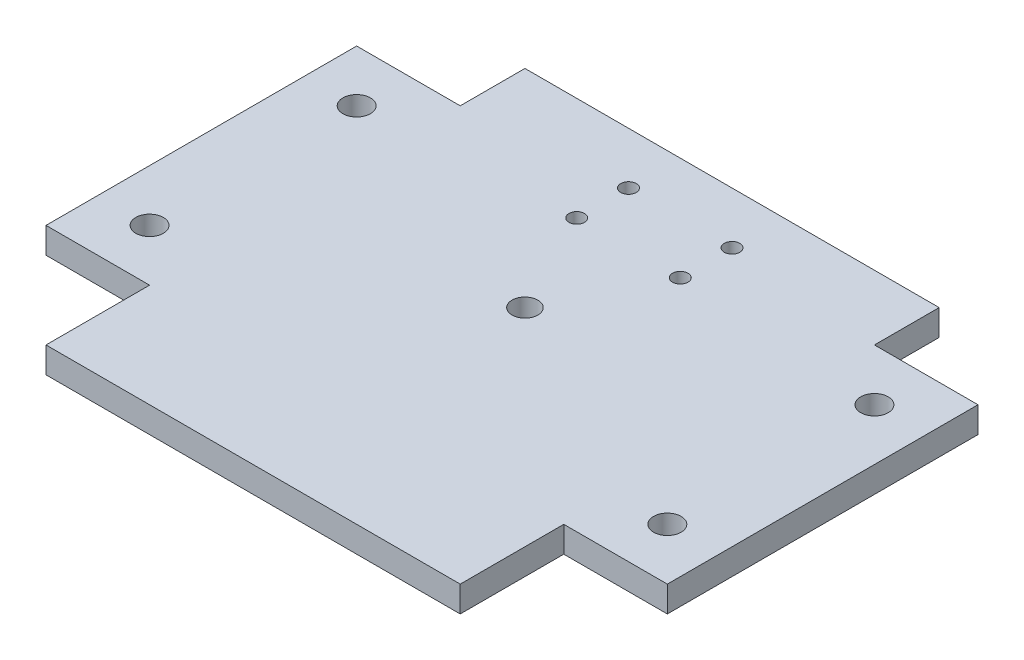
SolidWorks part; units mm, degrees
ref_plane "Front Plane" through (0, 0, 0) normal (0, 0, 1) x (1, 0, 0)
ref_plane "Top Plane" through (0, 0, 0) normal (0, 1, 0) x (1, 0, 0)
ref_plane "Right Plane" through (0, 0, 0) normal (1, 0, 0) x (0, 0, -1)
sketch "Sketch1" plane through (0, 0, 0) normal (0, 1, 0) x (1, 0, 0)
  line L0 (63.5, 104.775) -> (88.9, 104.775) construction
  line L1 (0, 0) -> (152.4, 0)
  line L2 (0, 0) -> (0, 117.475)
  line L3 (0, 117.475) -> (152.4, 117.475)
  line L4 (152.4, 0) -> (152.4, 117.475)
  line L7 (0, 101.6) -> (25.4, 101.6)
  line L8 (25.4, 117.475) -> (25.4, 101.6)
  line L11 (0, 25.4) -> (25.4, 25.4)
  line L12 (25.4, 0) -> (25.4, 25.4)
  line L15 (152.4, 101.6) -> (127, 101.6)
  line L16 (127, 117.475) -> (127, 101.6)
  line L19 (152.4, 25.4) -> (127, 25.4)
  line L20 (127, 0) -> (127, 25.4)
  line L21 (88.9, 104.775) -> (88.9, 92.075) construction
  line L22 (88.9, 92.075) -> (63.5, 92.075) construction
  line L23 (63.5, 92.075) -> (63.5, 104.775) construction
  circle A0 centre (12.7, 88.9) radius 3.3782
  circle A1 centre (139.7, 88.9) radius 3.3782
  circle A2 centre (12.7, 38.1) radius 3.3782
  circle A3 centre (139.7, 38.1) radius 3.3782
  circle A4 centre (63.5, 104.775) radius 1.905
  circle A5 centre (88.9, 104.775) radius 1.905
  circle A6 centre (63.5, 92.075) radius 1.905
  circle A7 centre (88.9, 92.075) radius 1.905
  circle A8 centre (76.2, 66.675) radius 3.175
  point P30 (12.7, 25.4)
  point P32 (139.7, 25.4)
  point P35 (76.2, 117.475)
  point P36 (76.2, 104.775)
  point P39 (0, 0)
  point P40 (76.2, 92.075)
  point P41 (0, 0)
  point P42 (0, 0)
  point P43 (0, 0)
  point P44 (0, 0)
  point P45 (0, 0)
  point P46 (0, 0)
  point P47 (0, 0)
  point P48 (0, 0)
  dimension "D6" = 6.7564
  dimension "D8" = 3.81
  dimension "D12" = 6.35
  dimension "D1" = 152.4
  dimension "D2" = 117.475
  dimension "D3" = 15.875
  dimension "D4" = 12.7
  dimension "D5" = 12.7
  dimension "D7" = 25.4
  dimension "D9" = 25.4
  dimension "D10" = 12.7
  dimension "D11" = 12.7
  dimension "D13" = 25.4
extrude "Boss-Extrude1" add sketch "Sketch1" along normal blind 6.35
